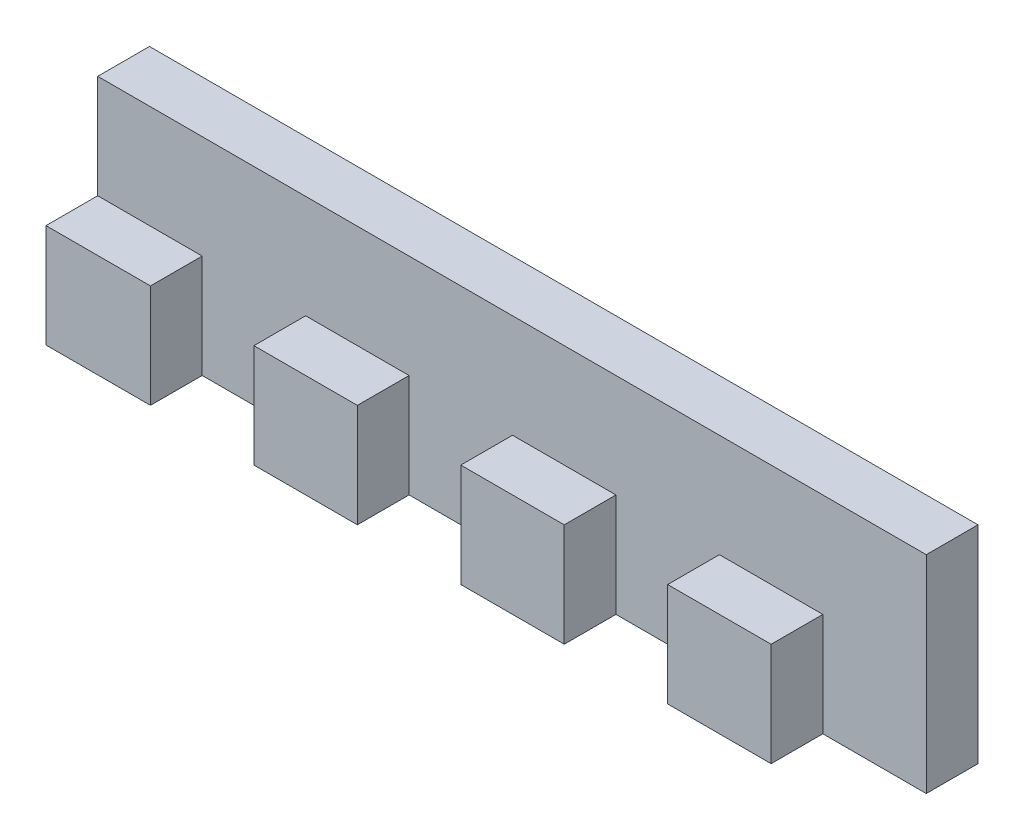
SolidWorks part; units mm, degrees
ref_plane "Спереди" through (0, 0, 0) normal (0, 0, 1) x (1, 0, 0)
ref_plane "Сверху" through (0, 0, 0) normal (0, 1, 0) x (1, 0, 0)
ref_plane "Справа" through (0, 0, 0) normal (1, 0, 0) x (0, 0, -1)
sketch "Эскиз1" plane through (0, 0, 0) normal (0, 1, 0) x (1, 0, 0)
  line L0 (0, 0) -> (10.0994, 0)
  line L1 (10.0994, 0) -> (10.0994, 5)
  line L2 (10.0994, 5) -> (20.0994, 5)
  line L3 (0, 10) -> (0, 0)
  line L4 (20.0994, 5) -> (20.0994, 0)
  line L5 (20.0994, 0) -> (30.0994, 0)
  line L13 (80.0994, 10) -> (0, 10)
  line L44 (80.0994, 5) -> (80.0994, 10)
  line L45 (30.0994, 0) -> (30.0994, 5)
  line L46 (30.0994, 5) -> (40.0994, 5)
  line L47 (40.0994, 5) -> (40.0994, 0)
  line L48 (40.0994, 0) -> (50.0994, 0)
  line L49 (50.0994, 0) -> (50.0994, 5)
  line L50 (50.0994, 5) -> (60.0994, 5)
  line L51 (60.0994, 5) -> (60.0994, 0)
  line L52 (60.0994, 0) -> (70.0994, 0)
  line L73 (70.0994, 0) -> (70.0994, 5)
  line L74 (70.0994, 5) -> (80.0994, 5)
  point P4 (69.2092, 0)
  dimension "D1" = 3
extrude "Бобышка-Вытянуть1" add sketch "Эскиз1" along normal blind 20
sketch "Эскиз2" plane through (0, 0, 0) normal (-1, 0, 0) x (0, 0, 1)
  line L0 (-10, 20) -> (0, 20) construction
  line L1 (-5, 20) -> (0, 20)
  line L2 (-5, 20) -> (-5, 10)
  line L3 (-5, 10) -> (0, 10)
  line L4 (0, 20) -> (0, 10)
  line L5 (0, 20) -> (0, 0) construction
extrude "Вырез-Вытянуть1" cut sketch "Эскиз2" against normal through all
